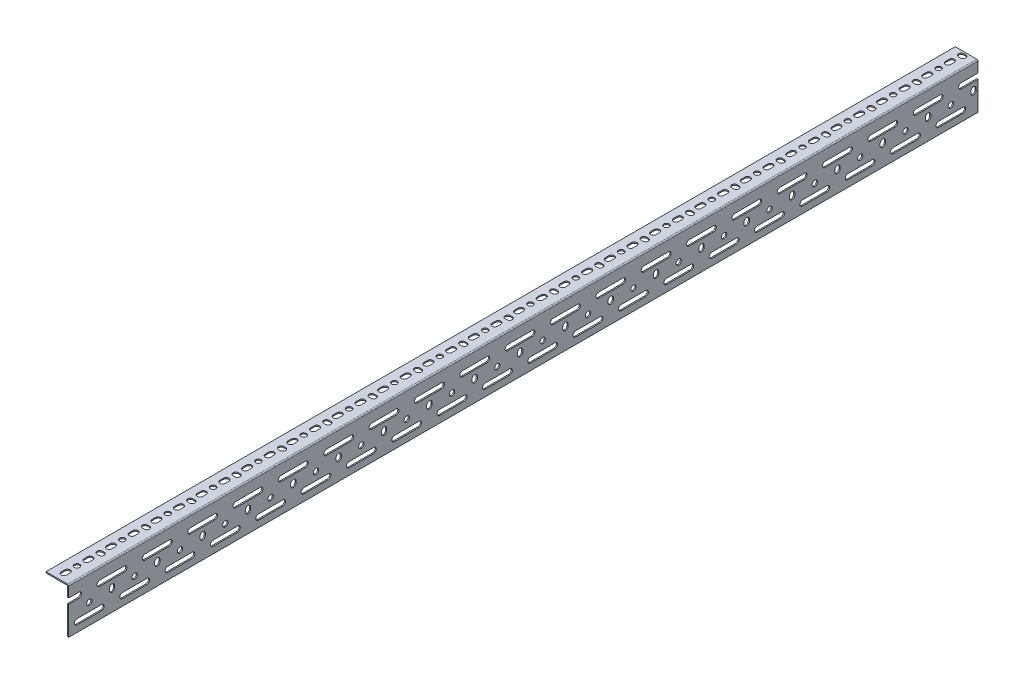
SolidWorks part; units mm, degrees
material "Black Iron Steel"
ref_plane "Front Plane" through (0, 0, 0) normal (0, 0, 1) x (1, 0, 0)
ref_plane "Top Plane" through (0, 0, 0) normal (0, 1, 0) x (1, 0, 0)
ref_plane "Right Plane" through (0, 0, 0) normal (1, 0, 0) x (0, 0, -1)
other "total length"
sketch "Sketch1" plane through (0, 0, 0) normal (0, 1, 0) x (1, 0, 0)
  line L0 (0, 0) -> (0, 1524)
  dimension "D1" = 1524
other "Structural Member1"
ref_plane "Plane1" through (0, 0, 0) normal (0, 0, 1) x (-1, 0, 0)
sketch "Sketch110" plane through (0, 0, 0) normal (0, 0, 1) x (-1, 0, 0)
  line L0 (0, 2) -> (0, 76.2)
  line L1 (0, 76.2) -> (1, 76.2)
  line L2 (2, 75.2) -> (2, 4)
  line L3 (4, 2) -> (37.1, 2)
  line L4 (38.1, 1) -> (38.1, 0)
  line L5 (38.1, 0) -> (2, 0)
  arc A0 (38.1, 1) -> (37.1, 2) centre (37.1, 1) ccw
  arc A1 (1, 76.2) -> (2, 75.2) centre (1, 75.2) cw
  arc A2 (4, 2) -> (2, 4) centre (4, 4) cw
  arc A3 (0, 2) -> (2, 0) centre (2, 2) ccw
  point P10 (20.05, 0)
  point P14 (0, 39.1)
  point P15 (2, 39.1)
  point P16 (20.05, 2)
  point P17 (2, 76.2)
  point P18 (38.1, 2)
  point P21 (0, 0)
  point P22 (0, 0)
  dimension "Radius_1" = 2
  dimension "D4" = 2
  dimension "D1" = 2
  dimension "H_leg" = 38.1
  dimension "D2" = 1
  dimension "D3" = 76.2
sketch "Sketch12" plane through (0, 0, 0) normal (0, 1, 0) x (1, 0, 0)
  line L0 (-20.6, 12.5) -> (-20.6, 18.5) construction
  line L1 (-25.1, 12.5) -> (-25.1, 18.5)
  line L2 (-16.1, 12.5) -> (-16.1, 18.5)
  line L3 (-38.1, 1524) -> (-38.1, 0) construction
  line L5 (-2, 0) -> (-38.1, 0) construction
  arc A0 (-25.1, 12.5) -> (-16.1, 12.5) centre (-20.6, 12.5) ccw
  arc A1 (-16.1, 18.5) -> (-25.1, 18.5) centre (-20.6, 18.5) ccw
  point P2 (-20.6, 15.5)
  dimension "D1" = 15
  dimension "D4" = 8
  dimension "D2" = 9
  dimension "D3" = 13
extrude "Slot 1.5" cut sketch "Sketch12" against normal through all
sketch "Sketch13" plane through (0, 0, 0) normal (0, 1, 0) x (1, 0, 0)
  line L0 (-20.6, 34.5) -> (-20.6, 15.5) construction
  circle A0 centre (-20.6, 34.5) radius 4.5
  arc A2 (-16.1, 18.5) -> (-25.1, 18.5) centre (-20.6, 18.5) ccw construction
  dimension "D1" = 7
  dimension "D2" = 9
extrude "Hole 1.5" cut sketch "Sketch13" against normal through all
sketch "Sketch18" plane through (0, 0, 0) normal (0, 1, 0) x (1, 0, 0)
  line L0 (-20.6, 72.5) -> (-17.6, 72.5) construction
  line L1 (-20.6, 77) -> (-17.6, 77)
  line L2 (-20.6, 68) -> (-17.6, 68)
  arc A0 (-20.6, 77) -> (-20.6, 68) centre (-20.6, 72.5) ccw
  arc A1 (-17.6, 68) -> (-17.6, 77) centre (-17.6, 72.5) ccw
  point P2 (-19.1, 72.5)
  dimension "D2" = 12
  dimension "D1" = 9
  dimension "D3" = 38
extrude "Vertical Slot 1.5" cut sketch "Sketch18" against normal through all
sketch "Sketch15" plane through (0, 0, 0) normal (1, 0, 0) x (0, 0, -1)
  line L0 (12.5, -58.7) -> (18.5, -58.7) construction
  line L1 (12.5, -54.2) -> (18.5, -54.2)
  line L2 (12.5, -63.2) -> (18.5, -63.2)
  line L6 (0, -76.2) -> (0, -2) construction
  line L7 (1524, -76.2) -> (0, -76.2) construction
  arc A0 (12.5, -54.2) -> (12.5, -63.2) centre (12.5, -58.7) ccw
  arc A1 (18.5, -63.2) -> (18.5, -54.2) centre (18.5, -58.7) ccw
  point P2 (15.5, -58.7)
  dimension "D1" = 15
  dimension "D3" = 8
  dimension "D2" = 9
  dimension "D4" = 13
extrude "Small Slot 2.5" [suppressed] cut sketch "Sketch15" against normal through all
sketch "Sketch14" plane through (0, 0, 0) normal (1, 0, 0) x (0, 0, -1)
  line L0 (14, -60.7) -> (55, -60.7) construction
  line L1 (14, -56.2) -> (55, -56.2)
  line L2 (14, -65.2) -> (55, -65.2)
  line L3 (1524, -76.2) -> (0, -76.2) construction
  line L7 (0, -76.2) -> (0, -2) construction
  arc A0 (14, -56.2) -> (14, -65.2) centre (14, -60.7) ccw
  arc A1 (55, -65.2) -> (55, -56.2) centre (55, -60.7) ccw
  point P2 (34.5, -60.7)
  dimension "D1" = 50
  dimension "D3" = 11
  dimension "D4" = 9.5
  dimension "D2" = 9
extrude "Long Slot 2.5" cut sketch "Sketch14" against normal through all
sketch "Sketch16" plane through (0, 0, 0) normal (1, 0, 0) x (0, 0, -1)
  line L2 (0, -76.2) -> (0, -2) construction
  line L4 (55, -56.2) -> (14, -56.2) construction
  circle A0 centre (34.5, -42.7) radius 4.5
  dimension "D1" = 9
  dimension "D2" = 9
  dimension "D3" = 30
extrude "Hole 2.5" cut sketch "Sketch16" against normal through all
sketch "Sketch17" plane through (0, 0, 0) normal (1, 0, 0) x (0, 0, -1)
  line L0 (72.5, -39.7) -> (72.5, -42.7) construction
  line L1 (77, -39.7) -> (77, -42.7)
  line L2 (68, -39.7) -> (68, -42.7)
  line L3 (72.5, -42.7) -> (34.5, -42.7) construction
  arc A0 (77, -39.7) -> (68, -39.7) centre (72.5, -39.7) ccw
  arc A1 (68, -42.7) -> (77, -42.7) centre (72.5, -42.7) ccw
  point P2 (72.5, -41.2)
  dimension "D1" = 12
  dimension "D2" = 9
  dimension "D3" = 38
extrude "Vertical Slot 2.5" cut sketch "Sketch17" against normal through all
sketch "Sketch112" plane through (0, 0, 0) normal (1, 0, 0) x (0, 0, -1)
  line L0 (52, -23.7) -> (93, -23.7) construction
  line L1 (52, -19.2) -> (93, -19.2)
  line L2 (52, -28.2) -> (93, -28.2)
  line L3 (72.5, -23.7) -> (72.5, -39.7) construction
  line L4 (55, -56.2) -> (14, -56.2) construction
  arc A0 (52, -19.2) -> (52, -28.2) centre (52, -23.7) ccw
  arc A1 (93, -28.2) -> (93, -19.2) centre (93, -23.7) ccw
  point P2 (72.5, -23.7)
  dimension "D1" = 50
  dimension "D2" = 9
  dimension "D3" = 28
extrude "Long Slot 2.5 (2)" cut sketch "Sketch112" against normal through all
pattern_linear "Short Slot pattern 1.5" count 40 spacing 38 along (0, 0, -1) of "Slot 1.5"
pattern_linear "Hole pattern" count 20 spacing 76 along (0, 0, -1) of "Hole 2.5", "Hole 1.5"
pattern_linear "Vert Slot Pattern" count 20 spacing 76 along (0, 0, -1) of "Vertical Slot 1.5", "Vertical Slot 2.5"
pattern_linear "Long Slot pattern" count 20 spacing 76 along (0, 0, -1) of "Long Slot 2.5"
pattern_linear "Long Slot Pattern (2)" count 20 spacing 76 along (0, 0, -1) count 2 spacing 76 along (0, 0, 1) of "Long Slot 2.5 (2)"
equation "\"D4@Sketch110\" = \"Radius_1@Sketch110\""
